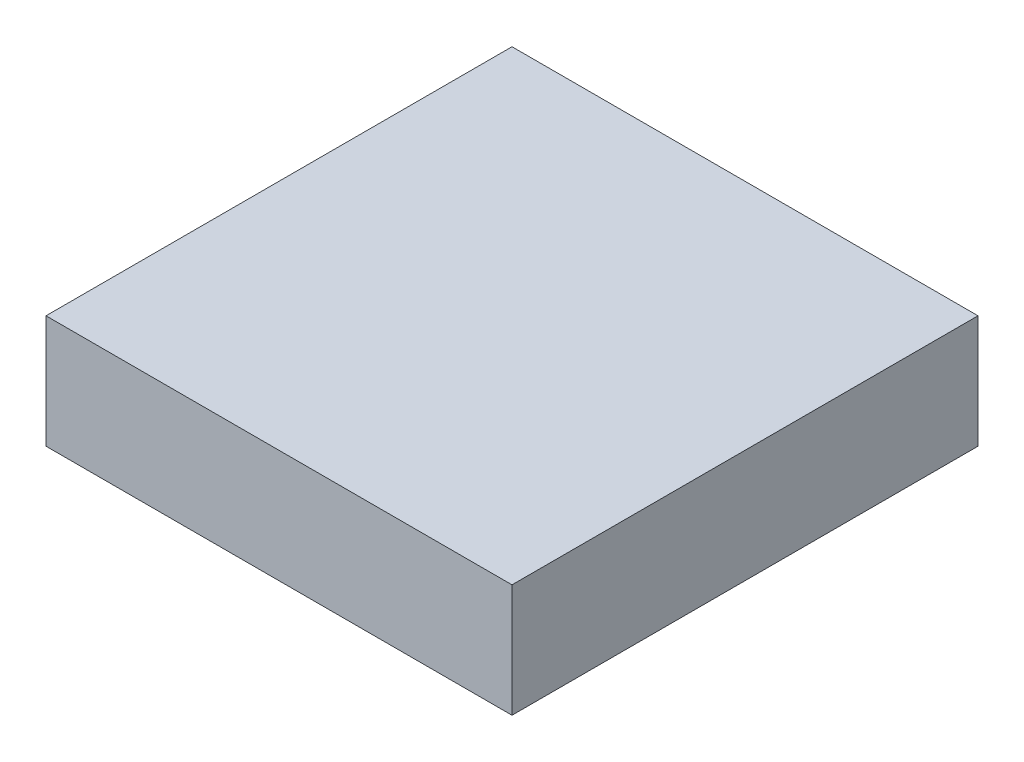
SolidWorks part; units mm, degrees
ref_plane "Front Plane" through (0, 0, 0) normal (0, 0, 1) x (1, 0, 0)
ref_plane "Top Plane" through (0, 0, 0) normal (0, 1, 0) x (1, 0, 0)
ref_plane "Right Plane" through (0, 0, 0) normal (1, 0, 0) x (0, 0, -1)
sketch "Sketch1" plane through (0, 0, 0) normal (0, 1, 0) x (1, 0, 0)
  line L1 (-10.4775, -10.4775) -> (10.4775, -10.4775)
  line L2 (-10.4775, -10.4775) -> (-10.4775, 10.4775)
  line L3 (-10.4775, 10.4775) -> (10.4775, 10.4775)
  line L4 (10.4775, -10.4775) -> (10.4775, 10.4775)
  line L5 (-10.4775, -10.4775) -> (10.4775, 10.4775) construction
  line L6 (-10.4775, 10.4775) -> (10.4775, -10.4775) construction
  point P0 (0, 0)
  dimension "D1" = 20.955
extrude "Boss-Extrude1" add sketch "Sketch1" along normal blind 5.08
